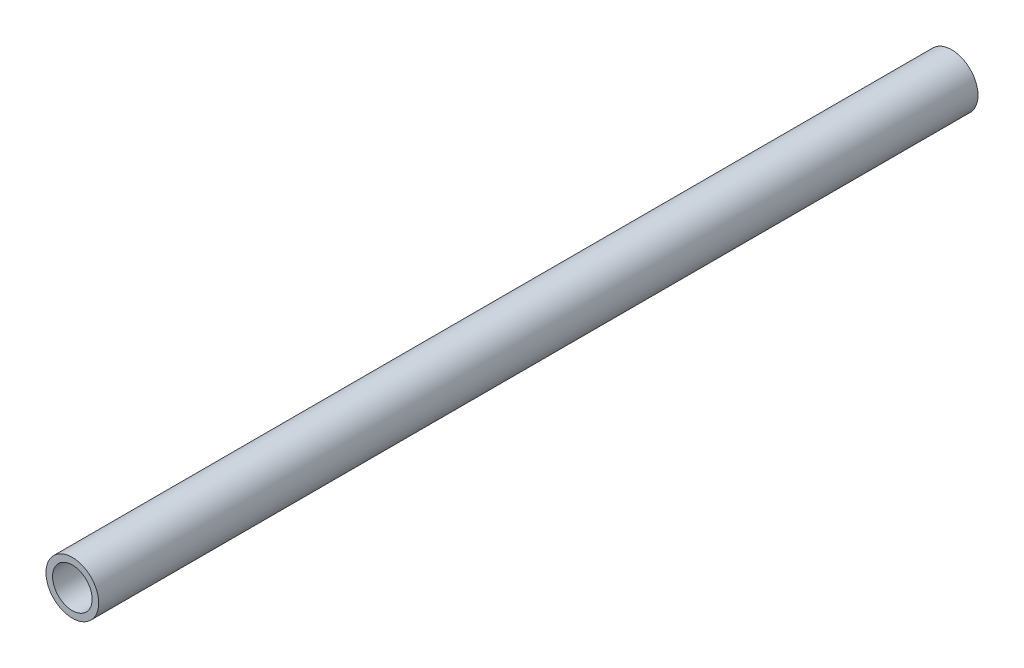
SolidWorks part; units mm, degrees
material "PVC Rígido"
ref_plane "Alzado" through (0, 0, 0) normal (0, 0, 1) x (1, 0, 0)
ref_plane "Planta" through (0, 0, 0) normal (0, 1, 0) x (1, 0, 0)
ref_plane "Vista lateral" through (0, 0, 0) normal (1, 0, 0) x (0, 0, -1)
sketch "Croquis1" plane through (0, 0, 0) normal (0, 0, 1) x (1, 0, 0)
  circle A0 centre (0, 0) radius 6
  dimension "D1" = 12
extrude "Saliente-Extruir1" add sketch "Croquis1" along normal mid plane 200
sketch "Croquis2" plane through (0, 0, 100) normal (0, 0, 1) x (1, 0, 0)
  circle A0 centre (0, 0) radius 4.5
  dimension "D1" = 9
extrude "Cortar-Extruir1" cut sketch "Croquis2" against normal through all
